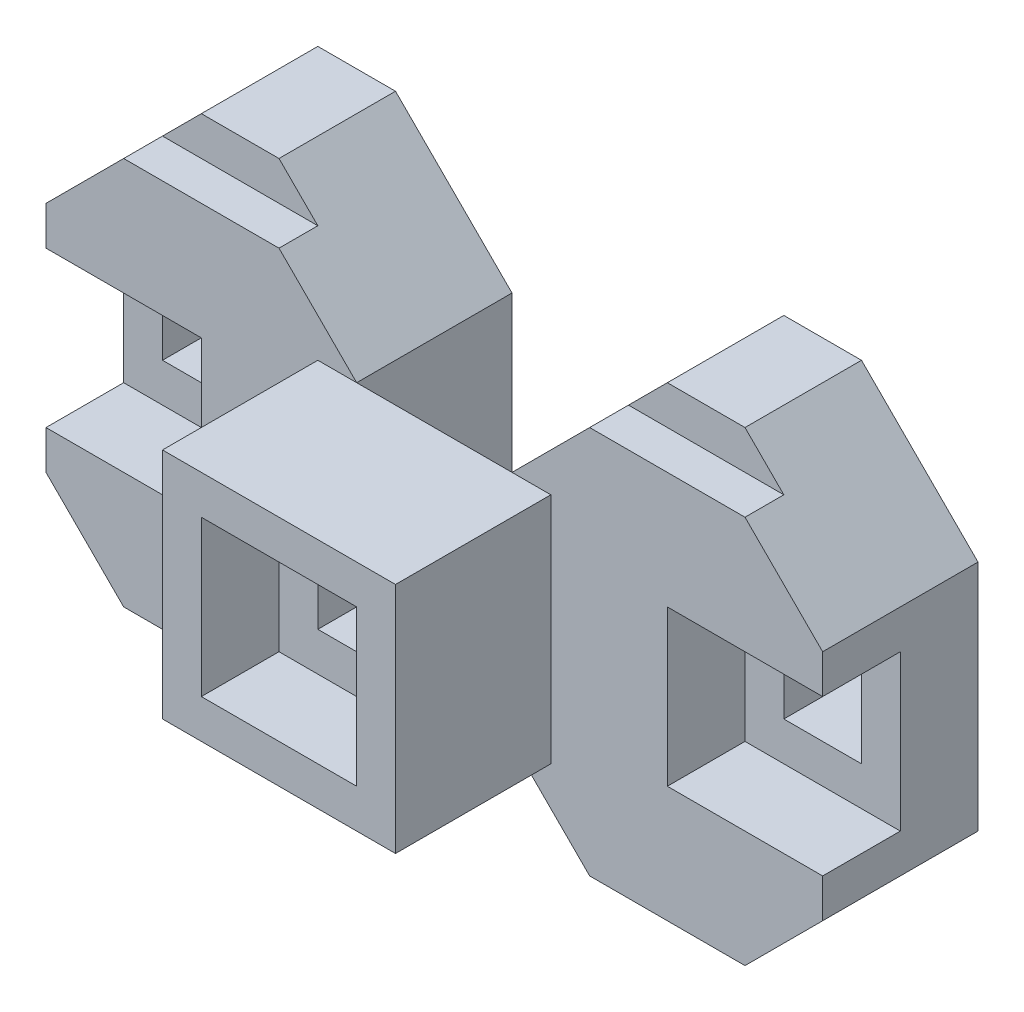
SolidWorks part; units mm, degrees
ref_plane "Front Plane" through (0, 0, 0) normal (0, 0, 1) x (1, 0, 0)
ref_plane "Top Plane" through (0, 0, 0) normal (0, 1, 0) x (1, 0, 0)
ref_plane "Right Plane" through (0, 0, 0) normal (1, 0, 0) x (0, 0, -1)
sketch "Sketch1" plane through (0, 0, 0) normal (0, 0, 1) x (1, 0, 0)
  line L0 (-40, 0) -> (-40, 30)
  line L1 (-40, 30) -> (-30, 40)
  line L2 (-30, 40) -> (-10, 40)
  line L3 (-10, 40) -> (0, 30)
  line L4 (0, 30) -> (0, 0)
  line L5 (0, 0) -> (-10, -10)
  line L6 (-10, -10) -> (-30, -10)
  line L7 (-30, -10) -> (-40, 0)
  dimension "D1" = 20
  dimension "D2" = 30
  dimension "D3" = 30
  dimension "D4" = 10
  dimension "D5" = 10
extrude "Boss-Extrude1" add sketch "Sketch1" along normal blind 20
sketch "Sketch2" plane through (0, 0, 20) normal (0, 0, 1) x (1, 0, 0)
  line L0 (-40, 25) -> (-20, 25)
  line L1 (-40, 30) -> (-40, 0) construction
  line L2 (-20, 25) -> (-20, 5)
  line L3 (-20, 5) -> (-40, 5)
  line L4 (-40, 5) -> (-40, 25)
  dimension "D1" = 20
  dimension "D2" = 20
  dimension "D3" = 5
extrude "Cut-Extrude1" cut sketch "Sketch2" against normal blind 10
sketch "Sketch3" plane through (0, 0, 10) normal (0, 0, 1) x (1, 0, 0)
  line L0 (-20, 25) -> (-40, 25) construction
  line L1 (-35, 10) -> (-25, 10)
  line L2 (-35, 10) -> (-35, 20)
  line L3 (-35, 20) -> (-25, 20)
  line L4 (-25, 10) -> (-25, 20)
  line L5 (-20, 5) -> (-20, 25) construction
  dimension "D1" = 10
  dimension "D2" = 10
  dimension "D3" = 15
  dimension "D4" = 5
extrude "Cut-Extrude2" cut sketch "Sketch3" against normal blind 194
sketch "Sketch5" plane through (0, 0, 0) normal (0, 0, -1) x (-1, 0, 0)
  line L0 (30, -10) -> (25, -15)
  line L1 (25, -15) -> (15, -15)
  line L2 (15, -15) -> (10, -10)
  line L3 (10, -10) -> (30, -10)
  line L4 (30, 40) -> (25, 45)
  line L5 (25, 45) -> (15, 45)
  line L6 (30, 40) -> (10, 40)
  line L7 (10, 40) -> (15, 45)
  dimension "D1" = 10
  dimension "D2" = 5
  dimension "D3" = 10
  dimension "D4" = 5
extrude "Boss-Extrude3" add sketch "Sketch5" against normal blind 15
sketch "Sketch6" plane through (0, 0, 20) normal (0, 0, 1) x (1, 0, 0)
  line L0 (-5, 30) -> (25, 30)
  line L1 (25, 30) -> (25, 0)
  line L2 (25, 0) -> (-5, 0)
  line L3 (-5, 0) -> (-5, 30)
  line L5 (0, 0) -> (0, 30) construction
  dimension "D1" = 30
  dimension "D2" = 30
  dimension "D3" = 5
extrude "Boss-Extrude4" add sketch "Sketch6" along normal blind 20
sketch "Sketch7" plane through (0, 0, 40) normal (0, 0, 1) x (1, 0, 0)
  line L0 (25, 0) -> (25, 30) construction
  line L1 (0, 5) -> (20, 5)
  line L2 (0, 5) -> (0, 25)
  line L3 (0, 25) -> (20, 25)
  line L4 (20, 5) -> (20, 25)
  line L5 (25, 30) -> (-5, 30) construction
  dimension "D1" = 20
  dimension "D2" = 20
  dimension "D3" = 5
  dimension "D4" = 5
extrude "Cut-Extrude3" cut sketch "Sketch7" against normal blind 10
sketch "Sketch8" plane through (0, 0, 30) normal (0, 0, 1) x (1, 0, 0)
  line L0 (20, 25) -> (0, 25) construction
  line L1 (5, 10) -> (15, 10)
  line L2 (5, 10) -> (5, 20)
  line L3 (5, 20) -> (15, 20)
  line L4 (15, 10) -> (15, 20)
  line L5 (20, 5) -> (20, 25) construction
  dimension "D1" = 5
  dimension "D2" = 5
  dimension "D3" = 10
  dimension "D4" = 10
extrude "Cut-Extrude4" cut sketch "Sketch8" against normal blind 41
sketch "Sketch10" plane through (0, 0, 20) normal (0, 0, -1) x (-1, 0, 0)
  line L0 (-20, 30) -> (-30, 40)
  line L1 (-30, 40) -> (-50, 40)
  line L2 (-50, 40) -> (-60, 30)
  line L3 (-60, 30) -> (-60, 0)
  line L4 (-60, 0) -> (-50, -10)
  line L5 (-50, -10) -> (-30, -10)
  line L6 (-30, -10) -> (-20, 0)
  line L7 (-20, 0) -> (-20, 30)
  line L8 (-25, 30) -> (0, 30) construction
  dimension "D1" = 10
  dimension "D2" = 10
  dimension "D3" = 10
  dimension "D4" = 10
  dimension "D5" = 10
  dimension "D6" = 20
  dimension "D7" = 40
  dimension "D8" = 5
extrude "Boss-Extrude7" add sketch "Sketch10" along normal blind 20
sketch "Sketch11" plane through (0, 0, 0) normal (0, 0, -1) x (-1, 0, 0)
  line L0 (-30, 40) -> (-35, 45)
  line L1 (-35, 45) -> (-45, 45)
  line L2 (-45, 45) -> (-50, 40)
  line L3 (-30, -10) -> (-35, -15)
  line L4 (-35, -15) -> (-45, -15)
  line L5 (-45, -15) -> (-50, -10)
  line L6 (-50, -10) -> (-30, -10)
  line M3 (-30, 40) -> (-50, 40)
  dimension "D1" = 10
  dimension "D2" = 5
  dimension "D3" = 5
  dimension "D4" = 10
  dimension "D5" = 5
  dimension "D6" = 5
extrude "Boss-Extrude8" add sketch "Sketch11" against normal blind 15 contours L1 L2 L0 M3 | L6 L3 L4 L5
sketch "Sketch12" plane through (0, 0, 20) normal (0, 0, 1) x (1, 0, 0)
  line L0 (40, 25) -> (60, 25)
  line L1 (60, 30) -> (60, 0) construction
  line L2 (60, 25) -> (60, 5)
  line L3 (60, 5) -> (40, 5)
  line L4 (40, 5) -> (40, 25)
  dimension "D1" = 20
  dimension "D2" = 20
  dimension "D3" = 5
extrude "Cut-Extrude5" cut sketch "Sketch12" against normal blind 10
sketch "Sketch13" plane through (0, 0, 10) normal (0, 0, 1) x (1, 0, 0)
  line L0 (60, 25) -> (40, 25) construction
  line L1 (45, 10) -> (55, 10)
  line L2 (45, 10) -> (45, 20)
  line L3 (45, 20) -> (55, 20)
  line L4 (55, 10) -> (55, 20)
  line L5 (60, 5) -> (60, 25) construction
  point P4 (50, 25)
  dimension "D1" = 5
  dimension "D2" = 5
  dimension "D3" = 10
  dimension "D4" = 10
extrude "Cut-Extrude6" cut sketch "Sketch13" against normal blind 31
